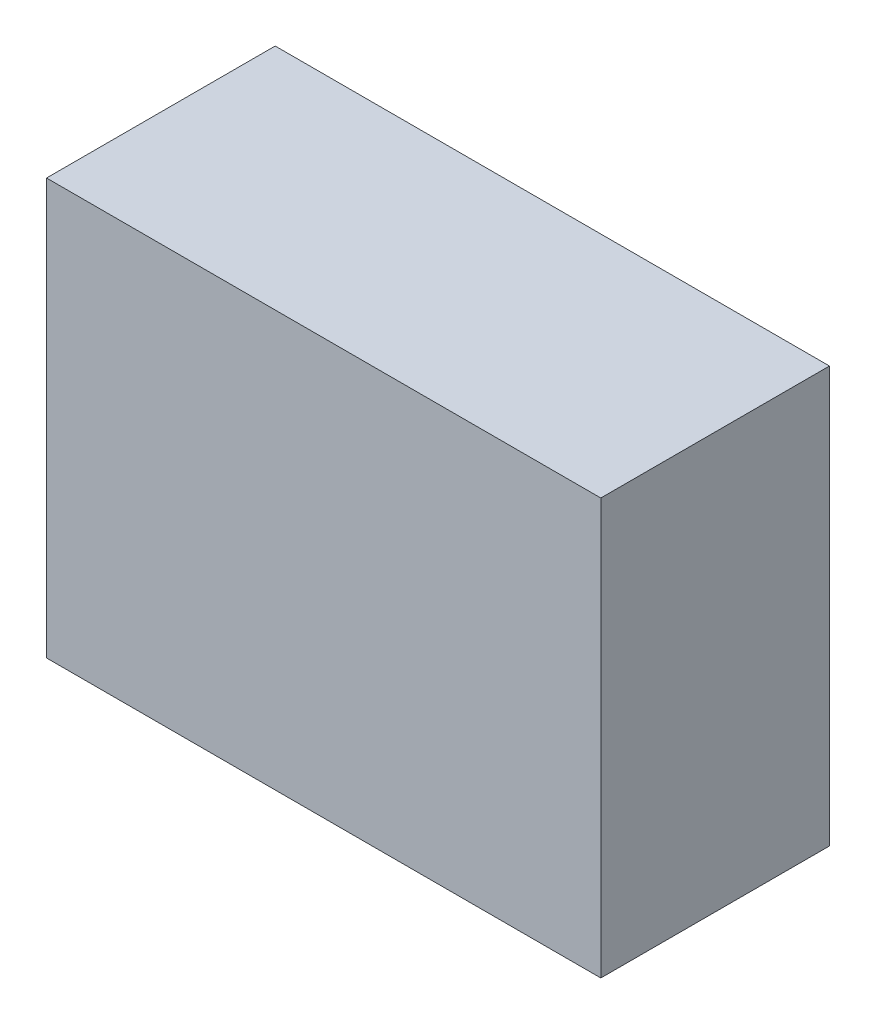
SolidWorks part; units mm, degrees
material "CA"
ref_plane "Front Plane" through (0, 0, 0) normal (0, 0, 1) x (1, 0, 0)
ref_plane "Top Plane" through (0, 0, 0) normal (0, 1, 0) x (1, 0, 0)
ref_plane "Right Plane" through (0, 0, 0) normal (1, 0, 0) x (0, 0, -1)
sketch "Sketch1" plane through (0, 0, 0) normal (0, 0, 1) x (1, 0, 0)
  line L1 (-223.5165, 146.1538) -> (176.4835, 146.1538)
  line L2 (-223.5165, 146.1538) -> (-223.5165, -153.8462)
  line L3 (-223.5165, -153.8462) -> (176.4835, -153.8462)
  line L4 (176.4835, 146.1538) -> (176.4835, -153.8462)
  dimension "D1" = 400
  dimension "D2" = 300
extrude "Boss-Extrude1" add sketch "Sketch1" along normal blind 165
